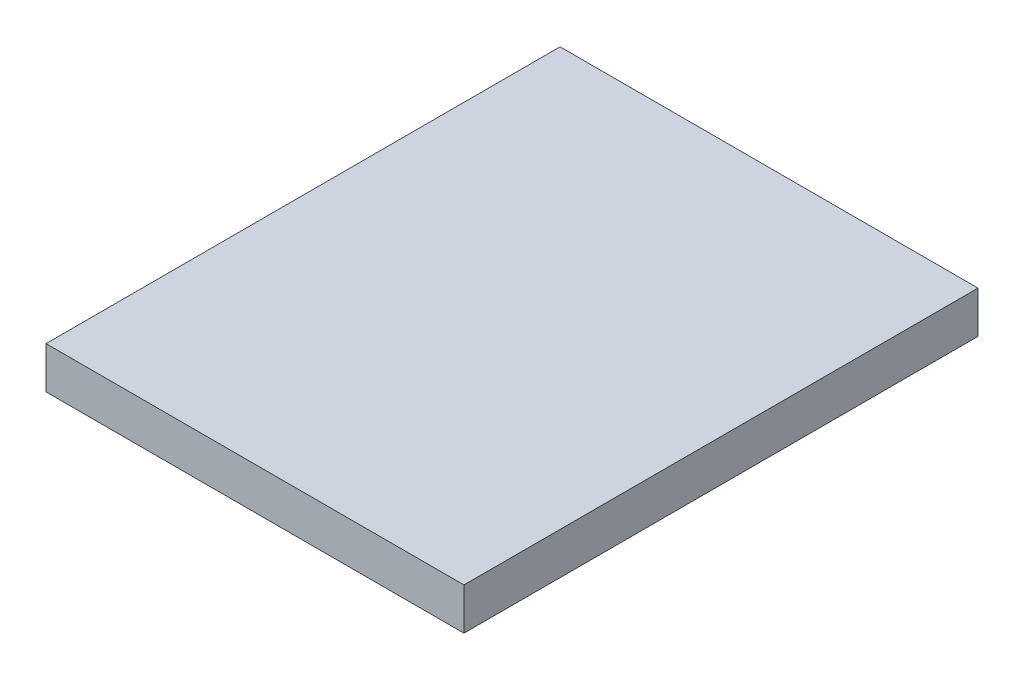
SolidWorks part; units mm, degrees
ref_plane "Front Plane" through (0, 0, 0) normal (0, 0, 1) x (1, 0, 0)
ref_plane "Top Plane" through (0, 0, 0) normal (0, 1, 0) x (1, 0, 0)
ref_plane "Right Plane" through (0, 0, 0) normal (1, 0, 0) x (0, 0, -1)
sketch "Sketch1" plane through (0, 0, 0) normal (0, 1, 0) x (1, 0, 0)
  line L1 (0, 0) -> (140, 0)
  line L2 (0, 0) -> (0, 12.3)
  line L3 (0, 12.3) -> (140, 12.3)
  line L4 (140, 0) -> (140, 12.3)
  dimension "D1" = 12.3
  dimension "D2" = 140
extrude "Boss-Extrude1" add sketch "Sketch1" along normal blind 1
sketch "Sketch2" plane through (0, 0, 0) normal (-1, 0, 0) x (0, 0, 1)
  line L1 (-12.3, 1) -> (0, 1)
  line L2 (-12.3, 1) -> (-12.3, 0)
  line L3 (-12.3, 0) -> (0, 0)
  line L4 (0, 1) -> (0, 0)
extrude "Cut-Extrude1" cut sketch "Sketch2" against normal blind 130
